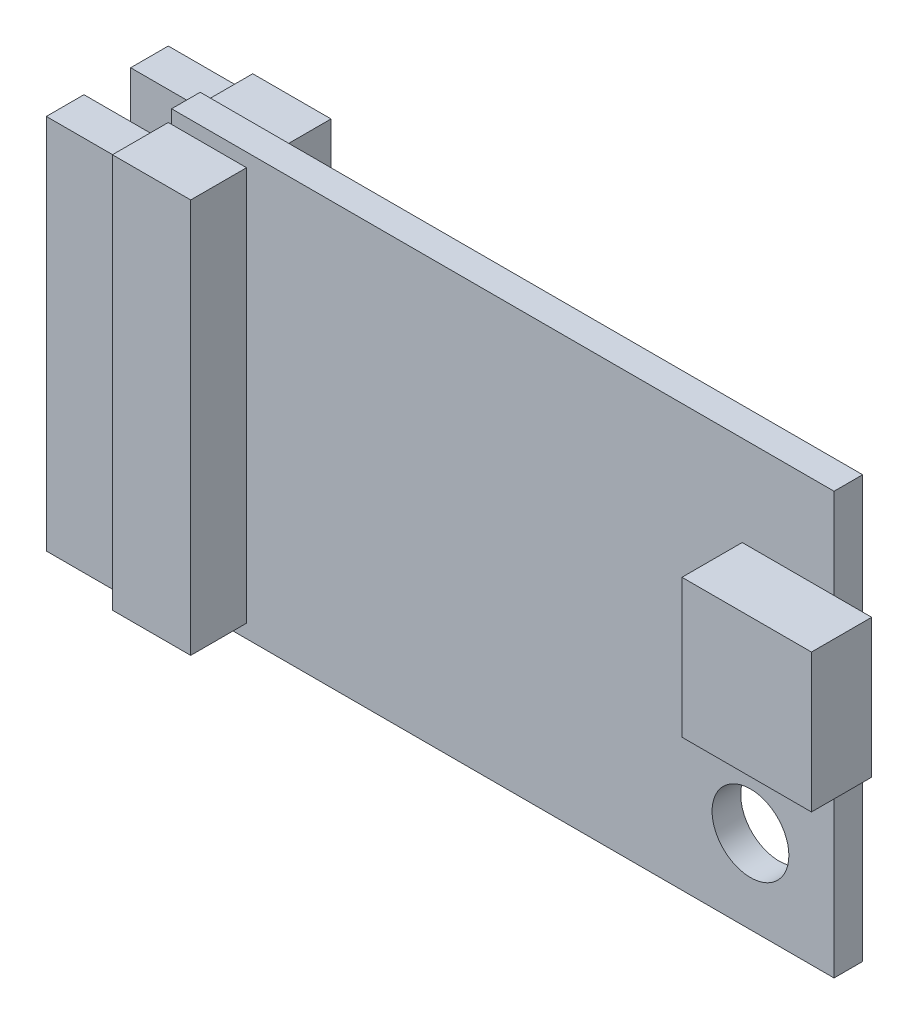
SolidWorks part; units mm, degrees
ref_plane "Front Plane" through (0, 0, 0) normal (0, 0, 1) x (1, 0, 0)
ref_plane "Top Plane" through (0, 0, 0) normal (0, 1, 0) x (1, 0, 0)
ref_plane "Right Plane" through (0, 0, 0) normal (1, 0, 0) x (0, 0, -1)
sketch "Sketch1" plane through (0, 0, 0) normal (0, 0, 1) x (1, 0, 0)
  line L1 (-11, 7) -> (11, 7)
  line L2 (-11, 7) -> (-11, -7)
  line L3 (-11, -7) -> (11, -7)
  line L4 (11, 7) -> (11, -7)
  line L5 (-11, 7) -> (11, -7) construction
  line L6 (-11, -7) -> (11, 7) construction
  circle A0 centre (8.225, -4.225) radius 1.275
  point P0 (0, 0)
  dimension "D3" = 1.5
  dimension "D5" = 2.55
  dimension "D1" = 14
  dimension "D2" = 22
  dimension "D4" = 1.5
extrude "Boss-Extrude1" add sketch "Sketch1" along normal mid plane 0.95
sketch "Sketch2" plane through (0, 0, 0.475) normal (0, 0, 1) x (1, 0, 0)
  line L0 (-11, 7) -> (-11, -7) construction
  line L1 (-11.11, 6.55) -> (-8.51, 6.55)
  line L2 (-11.11, 6.55) -> (-11.11, -6.55)
  line L3 (-11.11, -6.55) -> (-8.51, -6.55)
  line L4 (-8.51, 6.55) -> (-8.51, -6.55)
  line L5 (-11.11, 6.55) -> (-8.51, -6.55) construction
  line L6 (-11.11, -6.55) -> (-8.51, 6.55) construction
  line L7 (-9.81, 0) -> (0, 0) construction
  point P0 (-9.81, 0)
  dimension "D1" = 13.1
  dimension "D2" = 2.6
  dimension "D3" = 0.11
extrude "Boss-Extrude2" add sketch "Sketch2" along normal blind 1.855
mirror "Mirror1" about plane through (0, 0, 0) normal (0, 0, 1) of "Boss-Extrude2"
sketch "Sketch3" plane through (-11.11, 0, 0) normal (-1, 0, 0) x (0, 0, 1)
  line L0 (0, 0) -> (-1.4, 0) construction
  line L1 (-0.775, 6.25) -> (-2.025, 6.25)
  line L2 (-0.775, 6.25) -> (-0.775, -6.25)
  line L3 (-0.775, -6.25) -> (-2.025, -6.25)
  line L4 (-2.025, 6.25) -> (-2.025, -6.25)
  line L5 (-0.775, 6.25) -> (-2.025, -6.25) construction
  line L6 (-0.775, -6.25) -> (-2.025, 6.25) construction
  point P0 (-1.4, 0)
  dimension "D1" = 1.4
  dimension "D2" = 1.25
  dimension "D3" = 12.5
extrude "Boss-Extrude3" add sketch "Sketch3" along normal blind 2.5
mirror "Mirror2" about plane through (0, 0, 0) normal (0, 0, 1) of "Boss-Extrude3"
sketch "Sketch4" plane through (0, 0, 0.475) normal (0, 0, 1) x (1, 0, 0)
  line L0 (11, -7) -> (11, 7) construction
  line L1 (12.25, 4) -> (7.95, 4)
  line L2 (12.25, 4) -> (12.25, -0.6)
  line L3 (12.25, -0.6) -> (7.95, -0.6)
  line L4 (7.95, 4) -> (7.95, -0.6)
  line L5 (12.25, 4) -> (7.95, -0.6) construction
  line L6 (12.25, -0.6) -> (7.95, 4) construction
  line L7 (11, 7) -> (-11, 7) construction
  point P0 (10.1, 1.7)
  dimension "D1" = 4.6
  dimension "D2" = 4.3
  dimension "D3" = 1.25
  dimension "D4" = 3
extrude "Boss-Extrude4" add sketch "Sketch4" along normal blind 2
